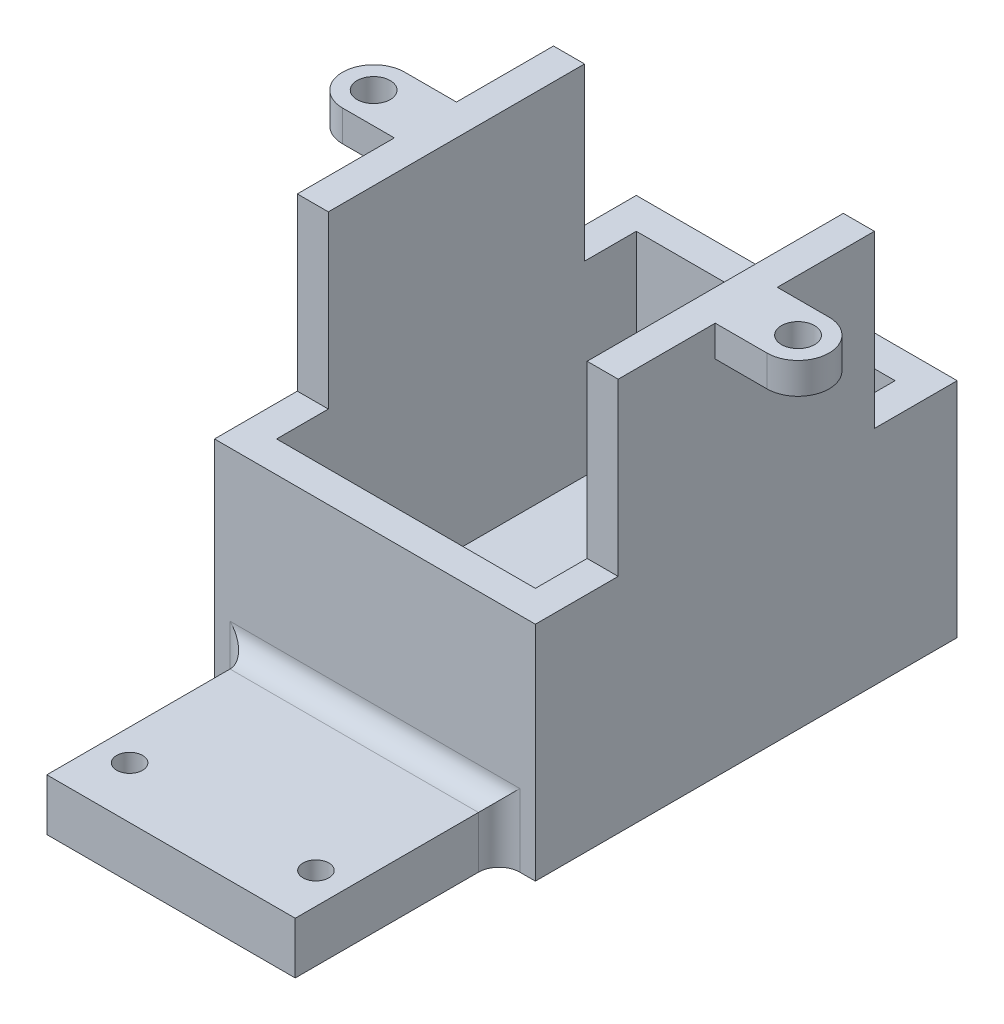
SolidWorks part; units mm, degrees
ref_plane "前视基准面" through (0, 0, 0) normal (0, 0, 1) x (1, 0, 0)
ref_plane "上视基准面" through (0, 0, 0) normal (0, 1, 0) x (1, 0, 0)
ref_plane "右视基准面" through (0, 0, 0) normal (1, 0, 0) x (0, 0, -1)
sketch "草图1" plane through (0, 0, 0) normal (0, 0, 1) x (1, 0, 0)
  line L1 (0, 0) -> (31, 0)
  line L2 (0, 0) -> (0, 38)
  line L3 (0, 38) -> (31, 38)
  line L4 (31, 0) -> (31, 38)
  dimension "D1" = 38
  dimension "D2" = 31
extrude "凸台-拉伸1" add sketch "草图1" against normal blind 40.75
sketch "草图2" plane through (31, 0, 0) normal (1, 0, 0) x (0, 0, -1)
  line L1 (40.75, 38) -> (32.75, 38)
  line L2 (40.75, 38) -> (40.75, 21.5)
  line L3 (40.75, 21.5) -> (32.75, 21.5)
  line L4 (32.75, 38) -> (32.75, 21.5)
  dimension "D1" = 16.5
  dimension "D2" = 8
extrude "切除-拉伸1" cut sketch "草图2" against normal blind 40.75
sketch "草图3" plane through (0, 38, 0) normal (0, 1, 0) x (1, 0, 0)
  line L0 (0, 40.75) -> (31, 0) construction
  line L1 (31, 40.75) -> (0, 40.75) construction
  line L2 (3, 3) -> (28, 3)
  line L3 (3, 3) -> (3, 37.75)
  line L4 (3, 37.75) -> (28, 37.75)
  line L5 (28, 3) -> (28, 37.75)
  line L6 (15.5, 37.75) -> (15.5, 3) construction
  line L7 (3, 20.375) -> (28, 20.375) construction
  line L8 (31, 32.75) -> (31, 0) construction
  point P4 (15.5, 20.375)
  dimension "D1" = 3
  dimension "D2" = 3
extrude "切除-拉伸2" cut sketch "草图3" against normal blind 34.5
sketch "草图4" plane through (0, 0, 0) normal (0, 0, 1) x (1, 0, 0)
  line L0 (31, 38) -> (0, 38) construction
  circle A0 centre (15.5, 38) radius 12.5
  dimension "D1" = 25
extrude "切除-拉伸3" cut sketch "草图4" against normal blind 34.5
sketch "草图5" plane through (0, 38, 0) normal (0, 1, 0) x (1, 0, 0)
  line L0 (0, 40.75) -> (31, 0) construction
  line L1 (15.5, 20.375) -> (15.5, 40.75) construction
  line L2 (15.5, 20.375) -> (31, 20.375) construction
  line L3 (31, 32.75) -> (31, 0) construction
  line L4 (36, 23.375) -> (31, 23.375)
  line L5 (31, 23.375) -> (31, 17.375)
  line L6 (31, 17.375) -> (36, 17.375)
  line L7 (0, 23.375) -> (0, 17.375)
  line L8 (0, 17.375) -> (-5, 17.375)
  line L9 (-5, 23.375) -> (0, 23.375)
  circle A0 centre (36, 20.375) radius 1.6
  arc A1 (36, 17.375) -> (36, 23.375) centre (36, 20.375) ccw
  arc A2 (-5, 17.375) -> (-5, 23.375) centre (-5, 20.375) cw
  circle A3 centre (-5, 20.375) radius 1.6
  dimension "D1" = 3.2
  dimension "D2" = 6
  dimension "D3" = 5
extrude "凸台-拉伸2" add sketch "草图5" against normal blind 3
sketch "草图6" plane through (0, 0, 0) normal (0, 0, 1) x (1, 0, 0)
  line L0 (31, 0) -> (31, 38) construction
  line L1 (0, 38) -> (31, 38)
  line L2 (0, 38) -> (0, 21.5)
  line L3 (0, 21.5) -> (31, 21.5)
  line L4 (31, 38) -> (31, 21.5)
  dimension "D1" = 16.5
extrude "切除-拉伸4" cut sketch "草图6" against normal blind 8
sketch "草图7" plane through (0, 0, 0) normal (0, 0, 1) x (1, 0, 0)
  line L0 (0, 0) -> (31, 0) construction
  line L1 (3.5, 0) -> (27.5, 0)
  line L2 (3.5, 0) -> (3.5, 5)
  line L3 (3.5, 5) -> (27.5, 5)
  line L4 (27.5, 0) -> (27.5, 5)
  line L5 (15.5, 21.5) -> (15.5, -5.2697) construction
  line L6 (0, 21.5) -> (31, 21.5) construction
  dimension "D1" = 24
  dimension "D2" = 5
extrude "凸台-拉伸3" add sketch "草图7" along normal blind 19.7
sketch "草图8" plane through (0, 5, 0) normal (0, 1, 0) x (1, 0, 0)
  circle A0 centre (6.5, -14.7) radius 1.25
  circle A1 centre (24.5, -14.7) radius 1.25
  point P4 (0, 0)
  point P5 (0, 0)
  dimension "D1" = 2.5
  dimension "D2" = 2.5
extrude "切除-拉伸5" cut sketch "草图8" against normal blind 20.7
fillet "圆角1" radius 2 3 edges at (27.5, 2.5, 0) (3.5, 2.5, 0) (15.5, 5, 0)
